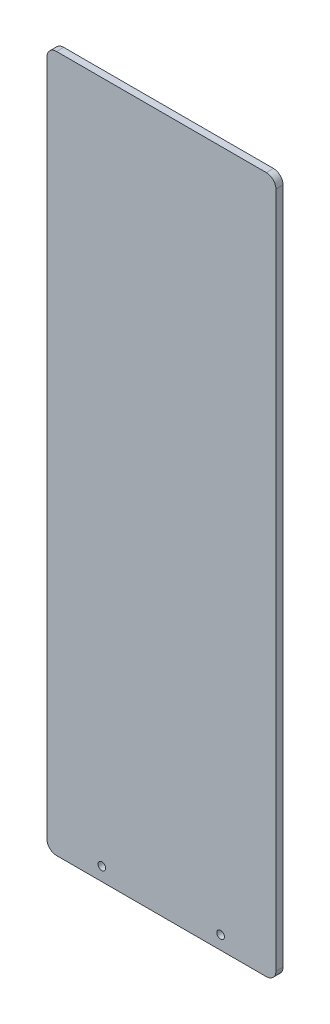
SolidWorks part; units mm, degrees
ref_plane "Front Plane" through (0, 0, 0) normal (0, 0, 1) x (1, 0, 0)
ref_plane "Top Plane" through (0, 0, 0) normal (0, 1, 0) x (1, 0, 0)
ref_plane "Right Plane" through (0, 0, 0) normal (1, 0, 0) x (0, 0, -1)
sketch "Sketch1" plane through (0, 0, 0) normal (0, 0, 1) x (1, 0, 0)
  line L1 (0, 463.55) -> (152.4, 463.55)
  line L2 (0, 463.55) -> (0, 0)
  line L3 (0, 0) -> (152.4, 0)
  line L4 (152.4, 463.55) -> (152.4, 0)
  dimension "D1" = 152.4
  dimension "D2" = 463.55
extrude "Boss-Extrude1" add sketch "Sketch1" along normal blind 4.7625
fillet "Fillet1" radius 6.35 4 edges at (152.4, 0, 2.3813) (0, 0, 2.3813) (152.4, 463.55, 2.3813) (0, 463.55, 2.3813)
sketch "Sketch2" plane through (0, 0, 4.7625) normal (0, 0, 1) x (1, 0, 0)
  circle A0 centre (115.57, 8.9535) radius 2.54
  circle A1 centre (36.533, 8.9535) radius 2.54
  dimension "D1" = 5.08
extrude "Cut-Extrude1" cut sketch "Sketch2" against normal blind 7.62
